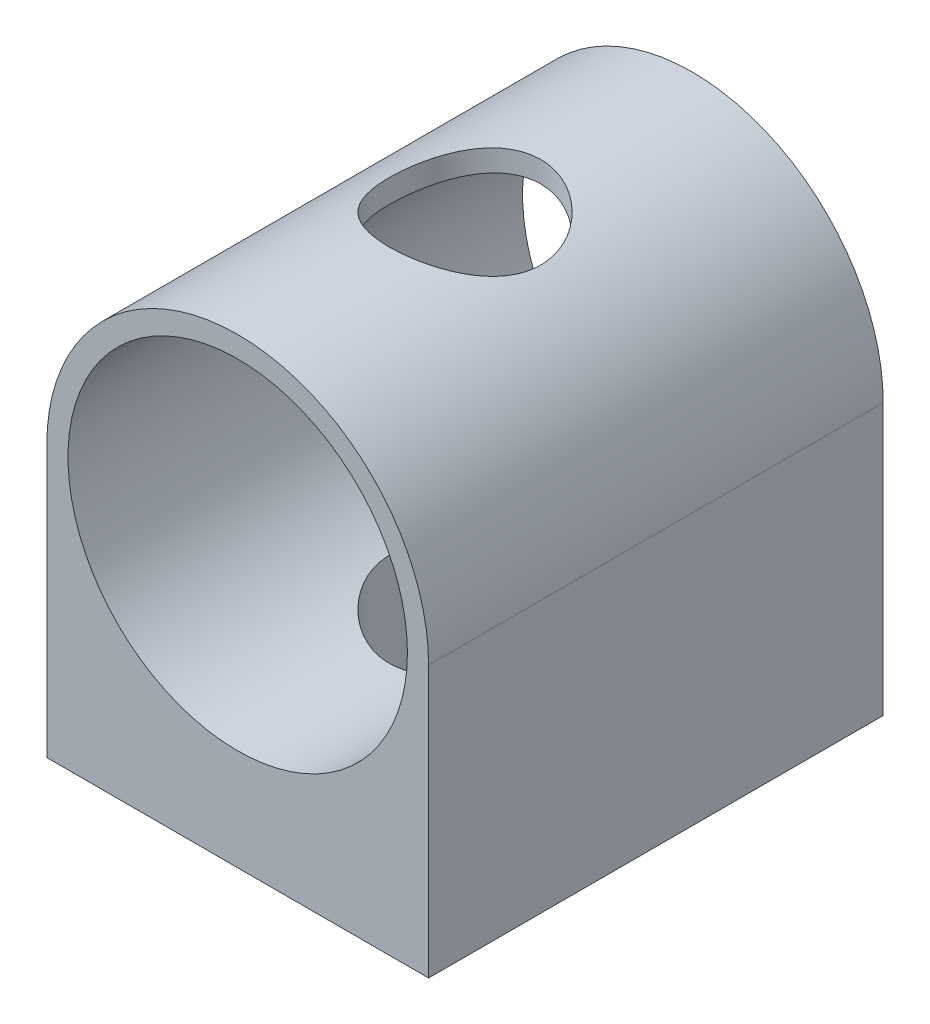
SolidWorks part; units mm, degrees
ref_plane "Front Plane" through (0, 0, 0) normal (0, 0, 1) x (1, 0, 0)
ref_plane "Top Plane" through (0, 0, 0) normal (0, 1, 0) x (1, 0, 0)
ref_plane "Right Plane" through (0, 0, 0) normal (1, 0, 0) x (0, 0, -1)
sketch "Sketch1" plane through (0, 0, 0) normal (0, 0, 1) x (1, 0, 0)
  line L0 (16, 0) -> (-16, 0)
  line L1 (-16, 0) -> (-16, 22.7096)
  line L2 (16, 0) -> (16, 22.7096)
  line L3 (-16, 22.7096) -> (16, 22.7096) construction
  arc A0 (-16, 22.7096) -> (16, 22.7096) centre (0, 22.7096) cw
  circle A1 centre (0, 22.7096) radius 14.224
  point P4 (0, 0)
  point P9 (0, 38.7096)
  dimension "D3" = 28.448
  dimension "D1" = 32
  dimension "D2" = 38.7096
extrude "Boss-Extrude1" add sketch "Sketch1" along normal blind 38.1 contours L3 L1 L0 L2 A1 | A0 L3 A1
sketch "Sketch2" plane through (0, 0, 0) normal (0, -1, 0) x (1, 0, 0)
  line L0 (0, 38.1) -> (0, 0) construction
  line L1 (16, 38.1) -> (-16, 38.1) construction
  line L2 (16, 19.05) -> (-16, 19.05) construction
  line L3 (16, 38.1) -> (16, 0) construction
  line L4 (-16, 38.1) -> (-16, 0) construction
  circle A0 centre (0, 19.05) radius 6.35
  point P14 (0, 19.05)
  dimension "D1" = 12.7
extrude "Cut-Extrude1" cut sketch "Sketch2" against normal through all
